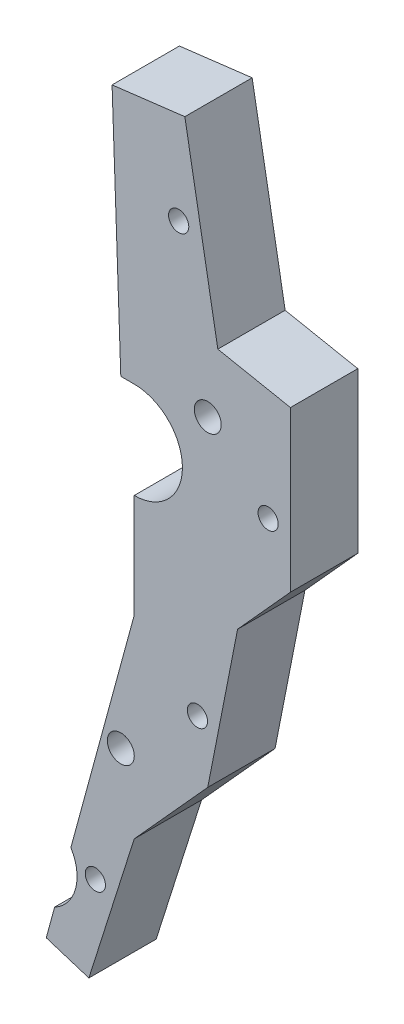
SolidWorks part; units mm, degrees
material "PMMA"
ref_plane "Front Plane" through (0, 0, 0) normal (0, 0, 1) x (1, 0, 0)
ref_plane "Top Plane" through (0, 0, 0) normal (0, 1, 0) x (1, 0, 0)
ref_plane "Right Plane" through (0, 0, 0) normal (1, 0, 0) x (0, 0, -1)
sketch "Sketch1" plane through (0, 0, 0) normal (0, 0, 1) x (1, 0, 0)
  line L0 (-54.3357, 25.8419) -> (-51.8868, 12.1157)
  line L1 (-51.8868, 12.1157) -> (-46.4956, 11.0567)
  line L2 (-46.4956, 11.0567) -> (-46.4956, -0.8192)
  line L3 (-46.4956, -0.8192) -> (-50.419, -5.16)
  line L4 (-50.419, -5.16) -> (-52.6347, -16.4399)
  line L5 (-52.6347, -16.4399) -> (-58.095, -22.4809)
  line L6 (-61.4619, -33.1128) -> (-58.095, -22.4809) construction
  line L7 (-58.095, -22.4809) -> (-52.6347, -16.4399) construction
  line L8 (-58.095, -22.4809) -> (-61.4619, -33.1128)
  line L9 (-61.4619, -33.1128) -> (-64.6271, -32.1104)
  line L10 (-64.6271, -32.1104) -> (-58.095, -8.1091)
  line L11 (-58.095, -8.1091) -> (-58.095, -0.3976)
  line L12 (-58.095, 6.7635) -> (-59.0905, 6.7635)
  line L13 (-59.0905, 6.7635) -> (-59.7388, 25.1845)
  line L14 (-59.7388, 25.1845) -> (-54.3357, 25.8419)
  arc A0 (-58.095, -0.3976) -> (-58.095, 6.7635) centre (-58.095, 3.183) ccw
  circle A1 centre (-54.7928, 18.9065) radius 0.75
  circle A2 centre (-48.15, 3.1) radius 0.75
  circle A3 centre (-53.3993, -12.2185) radius 0.75
  circle A4 centre (-60.9803, -26.5271) radius 0.75
  circle A5 centre (-52.6347, 7.376) radius 1
  circle A6 centre (-59.0905, -17.1588) radius 1
  point P42 (-64.5964, -32.0136)
  dimension "D1" = 1.5
  dimension "D2" = 2
  dimension "D3" = 2
extrude "Boss-Extrude1" add sketch "Sketch1" along normal blind 5
sketch "Sketch2" plane through (0, 0, 0) normal (0, 0, 1) x (1, 0, 0)
  circle A0 centre (-65.5, -27.0393) radius 3.162
extrude "Cut-Extrude3" cut sketch "Sketch2" along normal through all
